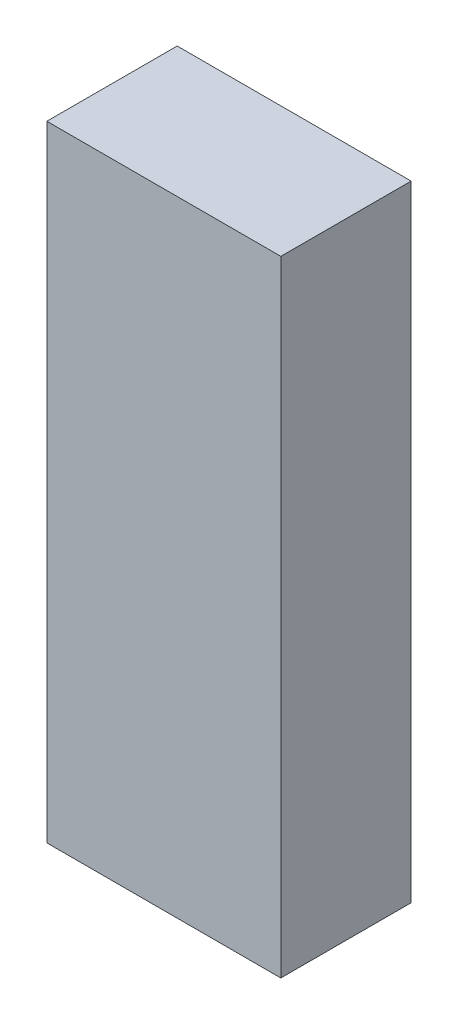
SolidWorks part; units mm, degrees
ref_plane "Front Plane" through (0, 0, 0) normal (0, 0, 1) x (1, 0, 0)
ref_plane "Top Plane" through (0, 0, 0) normal (0, 1, 0) x (1, 0, 0)
ref_plane "Right Plane" through (0, 0, 0) normal (1, 0, 0) x (0, 0, -1)
sketch "Sketch1" plane through (0, 0, 0) normal (0, 0, 1) x (1, 0, 0)
  line L1 (-114, 304.5) -> (114, 304.5)
  line L2 (-114, 304.5) -> (-114, -304.5)
  line L3 (-114, -304.5) -> (114, -304.5)
  line L4 (114, 304.5) -> (114, -304.5)
  line L5 (-114, 304.5) -> (114, -304.5) construction
  line L6 (-114, -304.5) -> (114, 304.5) construction
  point P0 (0, 0)
  dimension "D1" = 609
  dimension "D2" = 228
extrude "Boss-Extrude1" add sketch "Sketch1" along normal blind 127
